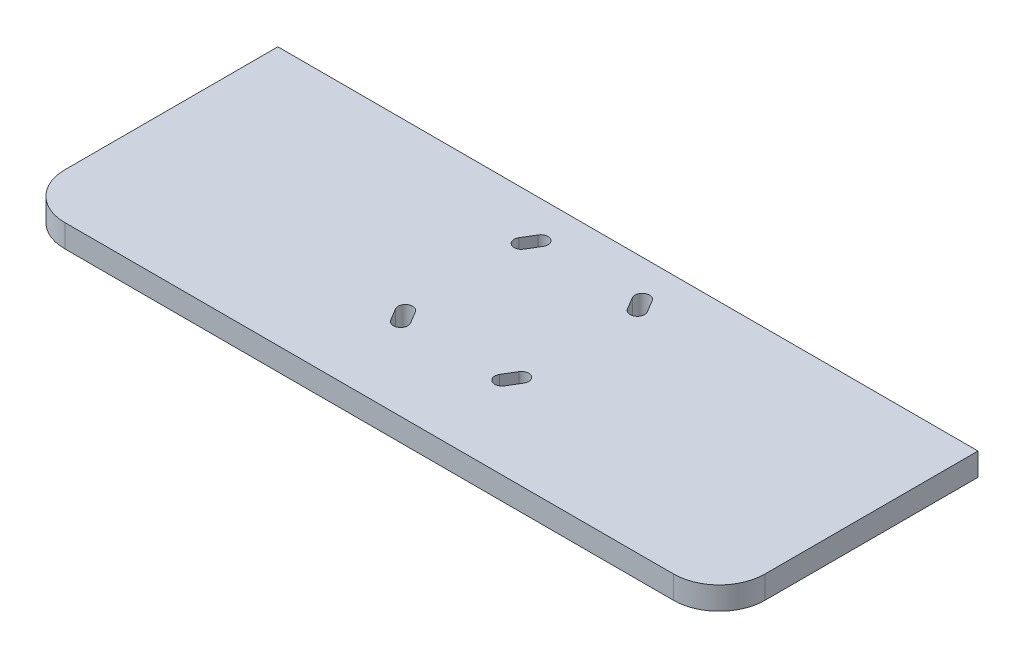
SolidWorks part; units mm, degrees
material "5052-H38, Rod (SS)"
ref_plane "Front Plane" through (0, 0, 0) normal (0, 0, 1) x (1, 0, 0)
ref_plane "Top Plane" through (0, 0, 0) normal (0, 1, 0) x (1, 0, 0)
ref_plane "Right Plane" through (0, 0, 0) normal (1, 0, 0) x (0, 0, -1)
sketch "Sketch1" plane through (0, 0, 0) normal (0, 1, 0) x (1, 0, 0)
  line L0 (230, 40) -> (-230, 40) construction
  line L1 (-200, -100) -> (200, -100)
  line L2 (-230, -70) -> (-230, 100)
  line L3 (-230, 100) -> (230, 100)
  line L4 (230, -70) -> (230, 100)
  line L5 (-230, -100) -> (230, 100) construction
  line L6 (-230, 100) -> (230, -100) construction
  line L7 (0, 40) -> (0, 100) construction
  arc A0 (-200, -100) -> (-230, -70) centre (-200, -70) cw
  arc A1 (200, -100) -> (230, -70) centre (200, -70) ccw
  point P0 (0, 0)
  dimension "D3" = 30
  dimension "D4" = 30
  dimension "D1" = 460
  dimension "D2" = 200
  dimension "D5" = 60
extrude "Boss-Extrude1" add sketch "Sketch1" along normal blind 15
sketch "Sketch3" plane through (0, 15, 0) normal (0, 1, 0) x (1, 0, 0)
  line L0 (-2468.9744, -5833.1453) -> (-2476.9119, -5837.9078) construction
  line L1 (-2466.5241, -5837.2291) -> (-2474.4616, -5841.9916)
  line L2 (-2471.4247, -5829.0614) -> (-2479.3622, -5833.8239)
  line L3 (-2430.8744, -5871.2453) -> (-2430.8744, -5820.4453) construction
  line L4 (-2430.8744, -5871.2453) -> (-2373.7244, -5871.2453) construction
  line L5 (-2468.9744, -5909.3453) -> (-2476.9119, -5904.5828) construction
  line L6 (-2466.5241, -5905.2614) -> (-2474.4616, -5900.4989)
  line L7 (-2471.4247, -5913.4291) -> (-2479.3622, -5908.6666)
  line L8 (-2392.7744, -5833.1453) -> (-2384.8369, -5837.9078) construction
  line L9 (-2395.2247, -5837.2291) -> (-2387.2872, -5841.9916)
  line L10 (-2390.3241, -5829.0614) -> (-2382.3866, -5833.8239)
  line L11 (-2392.7744, -5909.3453) -> (-2384.8369, -5904.5828) construction
  line L12 (-2395.2247, -5905.2614) -> (-2387.2872, -5900.4989)
  line L13 (-2390.3241, -5913.4291) -> (-2382.3866, -5908.6666)
  line L14 (-38.1, -38.1) -> (-33.3375, -46.0375) construction
  line L15 (-34.0162, -35.6497) -> (-29.2537, -43.5872)
  line L16 (-42.1838, -40.5503) -> (-37.4213, -48.4878)
  line L17 (0, 42.0687) -> (0, -42.0687) construction
  line L19 (38.1, -38.1) -> (33.3375, -46.0375) construction
  line L20 (34.0162, -35.6497) -> (29.2537, -43.5872)
  line L21 (42.1838, -40.5503) -> (37.4213, -48.4878)
  line L22 (-38.1, 38.1) -> (-33.3375, 46.0375) construction
  line L23 (-34.0162, 35.6497) -> (-29.2537, 43.5872)
  line L24 (-42.1838, 40.5503) -> (-37.4213, 48.4878)
  line L25 (38.1, 38.1) -> (33.3375, 46.0375) construction
  line L26 (34.0162, 35.6497) -> (29.2537, 43.5872)
  line L27 (42.1838, 40.5503) -> (37.4213, 48.4878)
  line L28 (35.7187, 42.0687) -> (-35.7187, 42.0687) construction
  line L29 (-35.7187, 42.0687) -> (-35.7187, -42.0687) construction
  line L30 (-35.7187, -42.0687) -> (35.7187, -42.0687) construction
  line L31 (35.7187, -42.0687) -> (35.7187, 42.0687) construction
  arc A0 (-2466.5241, -5837.2291) -> (-2471.4247, -5829.0614) centre (-2468.9744, -5833.1453) ccw
  arc A1 (-2479.3622, -5833.8239) -> (-2474.4616, -5841.9916) centre (-2476.9119, -5837.9078) ccw
  arc A2 (-2466.5241, -5905.2614) -> (-2471.4247, -5913.4291) centre (-2468.9744, -5909.3453) cw
  arc A3 (-2479.3622, -5908.6666) -> (-2474.4616, -5900.4989) centre (-2476.9119, -5904.5828) cw
  arc A4 (-2395.2247, -5837.2291) -> (-2390.3241, -5829.0614) centre (-2392.7744, -5833.1453) cw
  arc A5 (-2382.3866, -5833.8239) -> (-2387.2872, -5841.9916) centre (-2384.8369, -5837.9078) cw
  arc A6 (-2395.2247, -5905.2614) -> (-2390.3241, -5913.4291) centre (-2392.7744, -5909.3453) ccw
  arc A7 (-2382.3866, -5908.6666) -> (-2387.2872, -5900.4989) centre (-2384.8369, -5904.5828) ccw
  arc A8 (-34.0162, -35.6497) -> (-42.1838, -40.5503) centre (-38.1, -38.1) ccw
  arc A9 (-37.4213, -48.4878) -> (-29.2537, -43.5872) centre (-33.3375, -46.0375) ccw
  arc A10 (34.0162, -35.6497) -> (42.1838, -40.5503) centre (38.1, -38.1) cw
  arc A11 (37.4213, -48.4878) -> (29.2537, -43.5872) centre (33.3375, -46.0375) cw
  arc A12 (-34.0162, 35.6497) -> (-42.1838, 40.5503) centre (-38.1, 38.1) cw
  arc A13 (-37.4213, 48.4878) -> (-29.2537, 43.5872) centre (-33.3375, 46.0375) cw
  arc A14 (34.0162, 35.6497) -> (42.1838, 40.5503) centre (38.1, 38.1) ccw
  arc A15 (37.4213, 48.4878) -> (29.2537, 43.5872) centre (33.3375, 46.0375) ccw
  point P2 (-2472.9432, -5835.5265)
  point P12 (-2472.9432, -5906.964)
  point P19 (-2388.8057, -5835.5265)
  point P26 (-2388.8057, -5906.964)
  point P33 (-35.7187, -42.0687)
  point P40 (0, 0)
  point P43 (35.7187, -42.0687)
  point P50 (-35.7187, 42.0687)
  point P57 (35.7187, 42.0687)
  dimension "D1" = 84.1375
  dimension "D2" = 71.4375
extrude "Cut-Extrude2" cut sketch "Sketch3" against normal through all
sketch "Sketch4" plane through (0, 0, -100) normal (0, 0, -1) x (-1, 0, 0)
  line L1 (-262.2841, -47.4856) -> (262.2841, -47.4856)
  line L2 (-262.2841, -47.4856) -> (-262.2841, 47.4856)
  line L3 (-262.2841, 47.4856) -> (262.2841, 47.4856)
  line L4 (262.2841, -47.4856) -> (262.2841, 47.4856)
  line L5 (-262.2841, -47.4856) -> (262.2841, 47.4856) construction
  line L6 (-262.2841, 47.4856) -> (262.2841, -47.4856) construction
extrude "Cut-Extrude3" cut sketch "Sketch4" against normal blind 30
